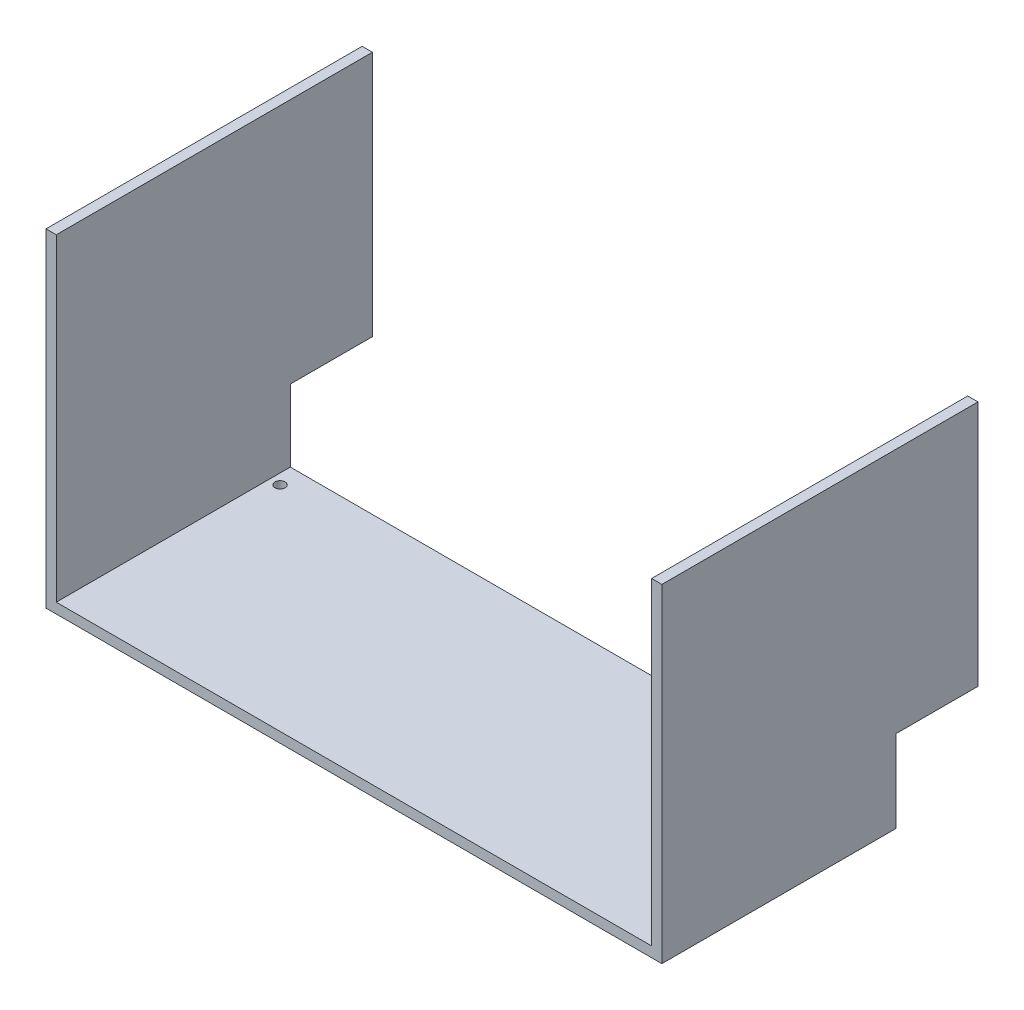
SolidWorks part; units mm, degrees
ref_plane "Front Plane" through (0, 0, 0) normal (0, 0, 1) x (1, 0, 0)
ref_plane "Top Plane" through (0, 0, 0) normal (0, 1, 0) x (1, 0, 0)
ref_plane "Right Plane" through (0, 0, 0) normal (1, 0, 0) x (0, 0, -1)
sketch "Sketch1" plane through (0, 0, 0) normal (0, 1, 0) x (1, 0, 0)
  line L1 (0, 0) -> (381, 0)
  line L2 (0, 0) -> (0, 429.26)
  line L3 (0, 429.26) -> (381, 429.26)
  line L4 (381, 0) -> (381, 429.26)
  dimension "D1" = 429.26
  dimension "D2" = 381
extrude "Boss-Extrude1" add sketch "Sketch1" along normal blind 6.35
sketch "Sketch2" plane through (0, 6.35, 0) normal (0, 1, 0) x (1, 0, 0)
  line L0 (0, 0) -> (381, 0) construction
  line L1 (63.5, 203.2) -> (317.5, 203.2)
  line L2 (63.5, 203.2) -> (63.5, 0)
  line L3 (63.5, 0) -> (317.5, 0)
  line L4 (317.5, 203.2) -> (317.5, 0)
  line L5 (381, 0) -> (381, 429.26) construction
  dimension "D1" = 254
  dimension "D2" = 203.2
  dimension "D3" = 0
  dimension "D4" = 63.5
extrude "Cut-Extrude1" cut sketch "Sketch2" against normal blind 6.35
sketch "Sketch3" plane through (0, 6.35, 0) normal (0, 1, 0) x (1, 0, 0)
  line L0 (381, 0) -> (381, 429.26) construction
  line L1 (0, 0) -> (381, 0)
  line L2 (0, 0) -> (0, 73.66)
  line L3 (0, 73.66) -> (381, 73.66)
  line L4 (381, 0) -> (381, 73.66)
  dimension "D1" = 73.66
extrude "Cut-Extrude2" cut sketch "Sketch3" against normal blind 6.35
sketch "Sketch4" plane through (0, 0, -203.2) normal (0, 0, 1) x (1, 0, 0)
  line L0 (317.5, 6.35) -> (63.5, 6.35) construction
  line L1 (63.5, 0) -> (317.5, 0)
  line L2 (63.5, 0) -> (63.5, 6.35)
  line L3 (63.5, 6.35) -> (317.5, 6.35)
  line L4 (317.5, 0) -> (317.5, 6.35)
  line L5 (63.5, 0) -> (63.5, 6.35) construction
  line L6 (317.5, 0) -> (63.5, 0) construction
  dimension "D1" = 254
  dimension "D2" = 0
  dimension "D3" = 0
extrude "Cut-Extrude3" cut sketch "Sketch4" against normal blind 73.66
sketch "Sketch6" plane through (0, 6.35, 0) normal (0, 1, 0) x (1, 0, 0)
  line L1 (381, 429.26) -> (374.65, 429.26)
  line L2 (381, 429.26) -> (381, 233.68)
  line L3 (381, 233.68) -> (374.65, 233.68)
  line L4 (374.65, 429.26) -> (374.65, 233.68)
  dimension "D1" = 6.35
  dimension "D2" = 195.58
extrude "Boss-Extrude2" add sketch "Sketch6" along normal blind 171.45
sketch "Sketch7" plane through (0, 6.35, 0) normal (0, 1, 0) x (1, 0, 0)
  line L1 (0, 429.26) -> (6.35, 429.26)
  line L2 (0, 429.26) -> (0, 233.68)
  line L3 (0, 233.68) -> (6.35, 233.68)
  line L4 (6.35, 429.26) -> (6.35, 233.68)
  dimension "D1" = 195.58
  dimension "D2" = 6.35
extrude "Boss-Extrude3" add sketch "Sketch7" along normal blind 158.75
sketch "Sketch8" plane through (0, 0, -429.26) normal (0, 0, -1) x (-1, 0, 0)
  line L1 (-6.35, 165.1) -> (0, 165.1)
  line L2 (-6.35, 165.1) -> (-6.35, 0)
  line L3 (-6.35, 0) -> (0, 0)
  line L4 (0, 165.1) -> (0, 0)
extrude "Boss-Extrude4" add sketch "Sketch8" along normal blind 50.8
sketch "Sketch9" plane through (0, 0, -233.68) normal (0, 0, 1) x (1, 0, 0)
  line L1 (6.35, 165.1) -> (0, 165.1)
  line L2 (6.35, 165.1) -> (6.35, 6.35)
  line L3 (6.35, 6.35) -> (0, 6.35)
  line L4 (0, 165.1) -> (0, 6.35)
extrude "Cut-Extrude4" cut sketch "Sketch9" against normal blind 50.8
sketch "Sketch10" plane through (0, 0, -429.26) normal (0, 0, -1) x (-1, 0, 0)
  line L0 (-381, 0) -> (-6.35, 0) construction
  line L1 (-381, 177.8) -> (-374.1001, 177.8)
  line L2 (-381, 177.8) -> (-381, 0)
  line L3 (-381, 0) -> (-374.1001, 0)
  line L4 (-374.1001, 177.8) -> (-374.1001, 0)
extrude "Boss-Extrude5" add sketch "Sketch10" along normal blind 50.8
sketch "Sketch11" plane through (0, 0, -233.68) normal (0, 0, 1) x (1, 0, 0)
  line L1 (381, 6.35) -> (374.65, 6.35)
  line L2 (381, 6.35) -> (381, 177.8)
  line L3 (381, 177.8) -> (374.65, 177.8)
  line L4 (374.65, 6.35) -> (374.65, 177.8)
extrude "Cut-Extrude5" cut sketch "Sketch11" against normal blind 50.8
sketch "Sketch13" plane through (0, 0, -429.26) normal (0, 0, 1) x (1, 0, 0)
  line L1 (374.65, 177.8) -> (374.1001, 177.8)
  line L2 (374.65, 177.8) -> (374.65, 6.35)
  line L3 (374.65, 6.35) -> (374.1001, 6.35)
  line L4 (374.1001, 177.8) -> (374.1001, 6.35)
extrude "Cut-Extrude6" cut sketch "Sketch13" against normal blind 50.8
sketch "Sketch14" plane through (0, 0, -480.06) normal (0, 0, -1) x (-1, 0, 0)
  line L1 (-381, 177.8) -> (-374.1001, 177.8)
  line L2 (-381, 177.8) -> (-381, 0)
  line L3 (-381, 0) -> (-374.1001, 0)
  line L4 (-374.1001, 177.8) -> (-374.1001, 0)
extrude "Cut-Extrude7" cut sketch "Sketch14" against normal blind 50.8
sketch "Sketch15" plane through (0, 0, -480.06) normal (0, 0, -1) x (-1, 0, 0)
  line L1 (-6.35, 165.1) -> (0, 165.1)
  line L2 (-6.35, 165.1) -> (-6.35, 0)
  line L3 (-6.35, 0) -> (0, 0)
  line L4 (0, 165.1) -> (0, 0)
extrude "Cut-Extrude8" cut sketch "Sketch15" against normal blind 50.8
sketch "Sketch16" plane through (0, 177.8, 0) normal (0, 1, 0) x (1, 0, 0)
  line L1 (381, 284.48) -> (374.65, 284.48)
  line L2 (381, 284.48) -> (381, 429.26)
  line L3 (381, 429.26) -> (374.65, 429.26)
  line L4 (374.65, 284.48) -> (374.65, 429.26)
extrude "Boss-Extrude6" add sketch "Sketch16" along normal blind 25.4
sketch "Sketch17" plane through (0, 165.1, 0) normal (0, 1, 0) x (1, 0, 0)
  line L1 (6.35, 284.48) -> (0, 284.48)
  line L2 (6.35, 284.48) -> (6.35, 429.26)
  line L3 (6.35, 429.26) -> (0, 429.26)
  line L4 (0, 284.48) -> (0, 429.26)
extrude "Boss-Extrude7" add sketch "Sketch17" against normal blind 19.05
sketch "Sketch19" plane through (0, 0, -429.26) normal (0, 0, -1) x (-1, 0, 0)
  line L0 (0, 0) -> (0, 165.1) construction
  line L1 (-6.35, 190.5) -> (0, 190.5)
  line L2 (-6.35, 190.5) -> (-6.35, 50.8)
  line L3 (-6.35, 50.8) -> (0, 50.8)
  line L4 (0, 190.5) -> (0, 50.8)
  dimension "D1" = 139.7
extrude "Boss-Extrude8" add sketch "Sketch19" along normal blind 50.8
sketch "Sketch20" plane through (0, 190.5, 0) normal (0, 1, 0) x (1, 0, 0)
  line L1 (6.35, 284.48) -> (0, 284.48)
  line L2 (6.35, 284.48) -> (6.35, 480.06)
  line L3 (6.35, 480.06) -> (0, 480.06)
  line L4 (0, 284.48) -> (0, 480.06)
extrude "Boss-Extrude9" add sketch "Sketch20" against normal blind 31.75
sketch "Sketch21" plane through (0, 0, -429.26) normal (0, 0, -1) x (-1, 0, 0)
  line L0 (-374.65, 6.35) -> (-374.65, 203.2) construction
  line L1 (-381, 203.2) -> (-374.65, 203.2)
  line L2 (-381, 203.2) -> (-381, 63.5)
  line L3 (-381, 63.5) -> (-374.65, 63.5)
  line L4 (-374.65, 203.2) -> (-374.65, 63.5)
  dimension "D1" = 139.7
extrude "Boss-Extrude10" add sketch "Sketch21" along normal blind 50.8
sketch "Sketch22" plane through (0, 203.2, 0) normal (0, 1, 0) x (1, 0, 0)
  line L0 (374.65, 480.06) -> (374.65, 284.48) construction
  line L1 (381, 284.48) -> (374.65, 284.48)
  line L2 (381, 284.48) -> (381, 480.06)
  line L3 (381, 480.06) -> (374.65, 480.06)
  line L4 (374.65, 284.48) -> (374.65, 480.06)
extrude "Boss-Extrude11" add sketch "Sketch22" against normal blind 50.8
sketch "Sketch23" plane through (0, 63.5, 0) normal (0, -1, 0) x (1, 0, 0)
  line L1 (381, -480.06) -> (374.65, -480.06)
  line L2 (381, -480.06) -> (381, -429.26)
  line L3 (381, -429.26) -> (374.65, -429.26)
  line L4 (374.65, -480.06) -> (374.65, -429.26)
extrude "Boss-Extrude12" add sketch "Sketch23" along normal blind 12.7
sketch "Sketch24" plane through (0, 190.5, 0) normal (0, 1, 0) x (1, 0, 0)
  line L0 (0, 480.06) -> (6.35, 480.06) construction
  line L1 (6.35, 284.48) -> (0, 284.48)
  line L2 (6.35, 284.48) -> (6.35, 480.06)
  line L3 (6.35, 480.06) -> (0, 480.06)
  line L4 (0, 284.48) -> (0, 480.06)
extrude "Boss-Extrude13" add sketch "Sketch24" along normal blind 12.7
sketch "Sketch26" plane through (0, 6.35, 0) normal (0, 1, 0) x (1, 0, 0)
  line L1 (0, 73.66) -> (381, 73.66)
  line L2 (0, 73.66) -> (0, 284.48)
  line L3 (0, 284.48) -> (381, 284.48)
  line L4 (381, 73.66) -> (381, 284.48)
extrude "Cut-Extrude9" cut sketch "Sketch26" against normal blind 12.7
sketch "Sketch27" plane through (0, 6.35, 0) normal (0, 1, 0) x (1, 0, 0)
  line L0 (374.65, 429.26) -> (6.35, 429.26) construction
  line L1 (374.65, 429.26) -> (374.65, 284.48) construction
  circle A0 centre (368.3, 416.56) radius 3.175
  dimension "D1" = 6.35
  dimension "D2" = 12.7
  dimension "D3" = 6.35
extrude "Cut-Extrude10" cut sketch "Sketch27" against normal blind 635 contours A0
sketch "Sketch28" plane through (0, 6.35, 0) normal (0, 1, 0) x (1, 0, 0)
  line L0 (374.65, 429.26) -> (6.35, 429.26) construction
  line L1 (6.35, 284.48) -> (6.35, 429.26) construction
  circle A0 centre (12.7, 416.56) radius 3.175
  dimension "D1" = 6.35
  dimension "D2" = 12.7
  dimension "D3" = 6.35
extrude "Cut-Extrude11" cut sketch "Sketch28" against normal blind 635
